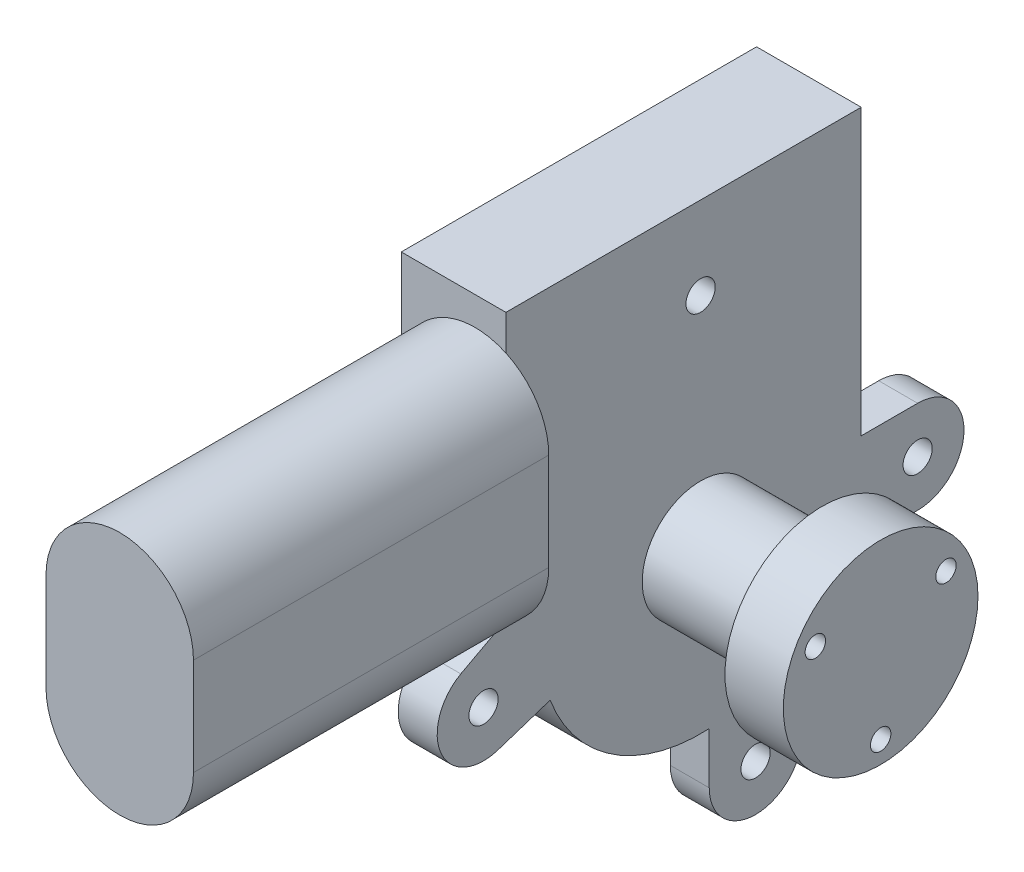
SolidWorks part; units mm, degrees
material "5052-H32"
ref_plane "Front Plane" through (0, 0, 0) normal (0, 0, 1) x (1, 0, 0)
ref_plane "Top Plane" through (0, 0, 0) normal (0, 1, 0) x (1, 0, 0)
ref_plane "Right Plane" through (0, 0, 0) normal (1, 0, 0) x (0, 0, -1)
other "Center of Mass"
sketch "Sketch1" plane through (0, 0, 0) normal (1, 0, 0) x (0, 0, -1)
  circle A0 centre (-33, 0) radius 33
  dimension "D1" = 66
extrude "Boss-Extrude1" add sketch "Sketch1" along normal blind 21.5
sketch "Sketch4" plane through (21.5, 0, 0) normal (1, 0, 0) x (0, 0, -1)
  circle A0 centre (-33, 0) radius 20
  dimension "D1" = 40
extrude "Boss-Extrude4" add sketch "Sketch4" along normal blind 37
sketch "Sketch6" plane through (0, 0, 0) normal (0, 0, 1) x (1, 0, 0)
  line L0 (21.5, -33) -> (21.5, 33) construction
  line L1 (0, 0) -> (21.5, 0)
  line L2 (0, 0) -> (0, 62)
  line L3 (0, 62) -> (21.5, 62)
  line L4 (21.5, 0) -> (21.5, 62)
  dimension "D1" = 62
extrude "Boss-Extrude5" add sketch "Sketch6" along normal blind 73
sketch "Sketch7" plane through (0, 0, 73) normal (0, 0, 1) x (1, 0, 0)
  line L0 (15.15, 41) -> (15.15, 21) construction
  line L1 (30.3, 41) -> (30.3, 21)
  line L2 (0, 41) -> (0, 21)
  line L3 (0, 62) -> (0, 0) construction
  arc A0 (30.3, 41) -> (0, 41) centre (15.15, 41) ccw
  arc A1 (0, 21) -> (30.3, 21) centre (15.15, 21) ccw
  point P2 (15.15, 31)
  point P19 (0, 31)
  dimension "D1" = 20
  dimension "D2" = 30.3
extrude "Boss-Extrude6" add sketch "Sketch7" along normal blind 73
sketch "Sketch9" plane through (21.5, 0, 0) normal (1, 0, 0) x (0, 0, -1)
  line L0 (-33, -33) -> (-33, 45) construction
  line L1 (11.6, 3.525) -> (0, 3.525)
  line L2 (0, 0) -> (0, 62) construction
  line L3 (11.6, -15.525) -> (-3.88, -15.525)
  line L4 (-12.175, -43.5) -> (-12.175, -25.5992)
  line L5 (-31.225, -32.9522) -> (-31.225, -43.5)
  line L6 (-82.2696, 2.3019) -> (-73, 7.245)
  line L7 (-74.6479, -15.056) -> (-63.9106, -11.5557)
  line L8 (-73, 7.245) -> (-63.9106, 7.245)
  line L9 (-63.9106, 7.245) -> (-63.9106, -11.5557)
  line L10 (-31.225, -32.9522) -> (-12.175, -25.5992)
  line L11 (0, 3.525) -> (-3.88, -15.525)
  arc A0 (-66, 0) -> (0, 0) centre (-33, 0) ccw construction
  arc A1 (11.6, 3.525) -> (11.6, -15.525) centre (11.6, -6) cw
  arc A2 (-12.175, -43.5) -> (-31.225, -43.5) centre (-21.7, -43.5) cw
  arc A3 (-82.2696, 2.3019) -> (-74.6479, -15.056) centre (-77.6, -6) ccw
  point P0 (11.6, -6)
  point P1 (-21.7, -43.5)
  point P2 (-77.6, -6)
  point P3 (-33, 45)
  point P22 (-63.9106, -11.5557)
  dimension "D1" = 44.6
  dimension "D5" = 44.6
  dimension "D7" = 45
  dimension "D8" = 9.525
  dimension "D9" = 9.525
  dimension "D10" = 9.525
  dimension "D2" = 6
  dimension "D3" = 11.3
  dimension "D4" = 43.5
  dimension "D6" = 6
extrude "Boss-Extrude7" add sketch "Sketch9" against normal blind 8
hole_wizard "M6x1.0 Tapped Hole1" positions "Sketch10" profile "Sketch11" tap size "M6x1.0" standard "ANSI Metric"
sketch "Sketch10" plane through (21.5, 0, 0) normal (1, 0, 0) x (0, 0, -1)
  point P0 (-33, 45)
  point P3 (11.6, -6)
  point P6 (-21.7, -43.5)
  point P9 (-77.6, -6)
  point P12 (-77.6, -6)
sketch "Sketch11" plane through (21.5, 45, 33) normal (0, 1, 0) x (0, 0, -1)
  line L0 (0, 0) -> (0, 16.4922)
  line L1 (0, 16.4922) -> (2.5, 14.99)
  line L2 (2.5, 14.99) -> (2.5, 11.94)
  line L3 (2.5, 11.94) -> (3, 11.94)
  line L4 (3, 11.94) -> (3, 0)
  line L5 (3, 0) -> (0, 0)
  line L10 (0, 16.4922) -> (-2.5, 14.99) construction
  line L11 (0, -6.35) -> (0, 107.95) construction
  dimension "Tap Drill Dia." = 5
  dimension "Tap Drill Depth" = 14.99
  dimension "Thread Major Dia." = 6
  dimension "Thread Depth" = 11.94
  dimension "Drill Angle" = 118
hole_wizard "M5x0.8 Tapped Hole1" positions "Sketch12" profile "Sketch13" tap size "M5x0.8" standard "ANSI Metric"
sketch "Sketch12" plane through (58.5, 0, 0) normal (1, 0, 0) x (0, 0, -1)
  line L0 (-33, -33) -> (-33, 45) construction
  line L1 (-33, -15.5) -> (-33, 0) construction
  line L4 (-33, -0.3676) -> (-33, 0) construction
  line L5 (-33, 0) -> (-46.4234, 7.75) construction
  line L7 (-33, 0) -> (-19.5766, 7.75) construction
  circle A0 centre (-33, 0) radius 15.5 construction
  point P9 (-33, -15.5)
  point P10 (-46.4234, 7.75)
  point P12 (-19.5766, 7.75)
  dimension "D1" = 31
  dimension "D2" = 120
  dimension "D3" = 120
sketch "Sketch13" plane through (58.5, 7.75, 19.5766) normal (0, 1, 0) x (0, 0, -1)
  line L0 (0, 0) -> (0, 13.4538)
  line L1 (0, 13.4538) -> (2.1, 12.192)
  line L2 (2.1, 12.192) -> (2.1, 0)
  line L5 (2.1, 0) -> (0, 0)
  line L10 (0, 13.4538) -> (-2.1, 12.192) construction
  line L11 (0, -6.35) -> (0, 107.95) construction
  dimension "Tap Drill Dia." = 4.2
  dimension "Tap Drill Depth" = 12.192
  dimension "Drill Angle" = 118
cosmetic thread "Hole Thread5" parameters "D1"=9.906, "D2"=5
cosmetic thread "Hole Thread6" parameters "D1"=9.906, "D2"=5
cosmetic thread "Hole Thread7" parameters "D1"=9.906, "D2"=5
sketch "Sketch14" plane through (0, 0, 0) normal (0, 1, 0) x (1, 0, 0)
  line L0 (46.5, -53) -> (46.5, -45)
  line L1 (21.5, -53) -> (58.5, -53) construction
  line L2 (46.5, -45) -> (21.5, -45)
  line L3 (21.5, -45) -> (21.5, -53)
  line L4 (21.5, -53) -> (58.5, -53) construction
  line L5 (21.5, -53) -> (46.5, -53)
  line L6 (58.5, -53) -> (58.5, -13) construction
  line L7 (21.5, -53) -> (21.5, -13) construction
  line L8 (58.5, -33) -> (21.5, -33) construction
  dimension "D1" = 8
  dimension "D2" = 12
revolve "Cut-Revolve1" cut sketch "Sketch14" angle 360 about L8
